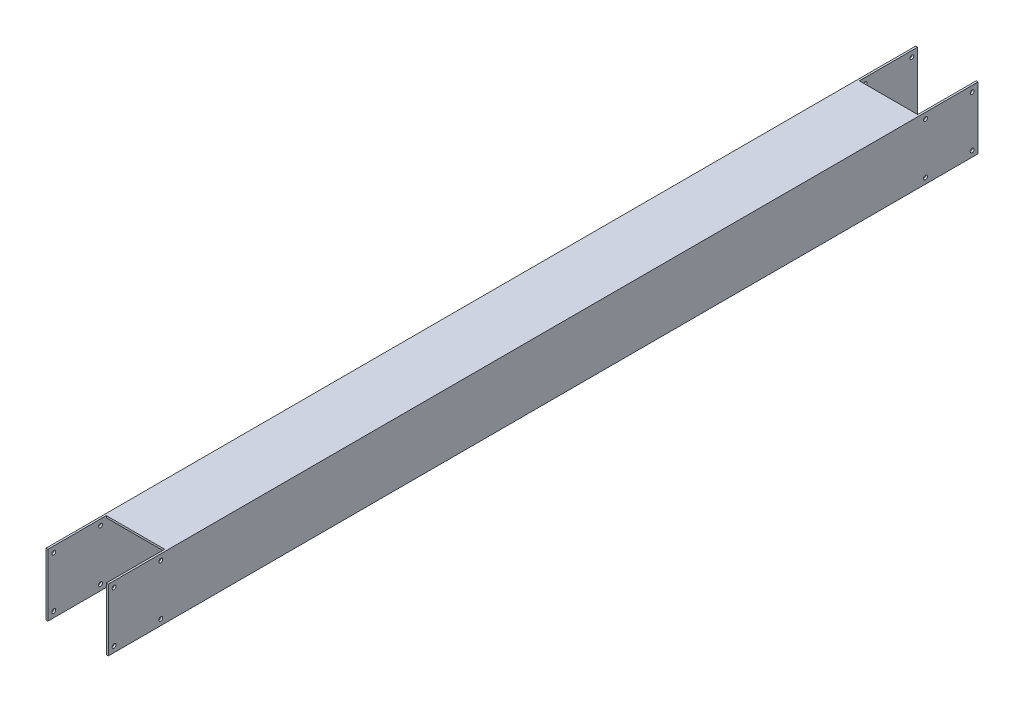
SolidWorks part; units mm, degrees
ref_plane "Front Plane" through (0, 0, 0) normal (0, 0, 1) x (1, 0, 0)
ref_plane "Top Plane" through (0, 0, 0) normal (0, 1, 0) x (1, 0, 0)
ref_plane "Right Plane" through (0, 0, 0) normal (1, 0, 0) x (0, 0, -1)
sketch "Sketch1" plane through (0, 0, 0) normal (0, 0, 1) x (1, 0, 0)
  line L0 (-150, 150) -> (150, 150)
  line L1 (-160, -160) -> (160, -160)
  line L2 (-160, -160) -> (-160, 160)
  line L3 (-160, 160) -> (160, 160)
  line L4 (160, -160) -> (160, 160)
  line L5 (-160, -160) -> (160, 160) construction
  line L6 (-160, 160) -> (160, -160) construction
  line L7 (150, -150) -> (150, 150)
  line L8 (-150, -150) -> (150, -150)
  line L9 (-150, -150) -> (-150, 150)
  point P0 (0, 0)
  dimension "D1" = 320
  dimension "D2" = 320
  dimension "D3" = 10
extrude "Boss-Extrude1" add sketch "Sketch1" along normal blind 4470
sketch "Sketch2" plane through (0, 0, 4470) normal (0, 0, 1) x (1, 0, 0)
  line L1 (150, -184.5332) -> (-150, -184.5332)
  line L2 (150, -184.5332) -> (150, 184.5332)
  line L3 (150, 184.5332) -> (-150, 184.5332)
  line L4 (-150, -184.5332) -> (-150, 184.5332)
  line L5 (150, -184.5332) -> (-150, 184.5332) construction
  line L6 (150, 184.5332) -> (-150, -184.5332) construction
  point P0 (0, 0)
extrude "Cut-Extrude1" cut sketch "Sketch2" against normal blind 300
sketch "Sketch3" plane through (160, 0, 0) normal (1, 0, 0) x (0, 0, -1)
  circle A0 centre (-4440, 130) radius 10
  circle A1 centre (-4200, 130) radius 10
  circle A2 centre (-4200, -130) radius 10
  circle A3 centre (-4440, -130) radius 10
  dimension "D2" = 20
extrude "Cut-Extrude2" cut sketch "Sketch3" against normal through all
ref_plane "Plane1" through (0, 0, 2235) normal (0, 0, -1) x (-1, 0, 0)
mirror "Mirror1" about plane through (0, 0, 2235) normal (0, 0, -1) of "Cut-Extrude1", "Cut-Extrude2"
